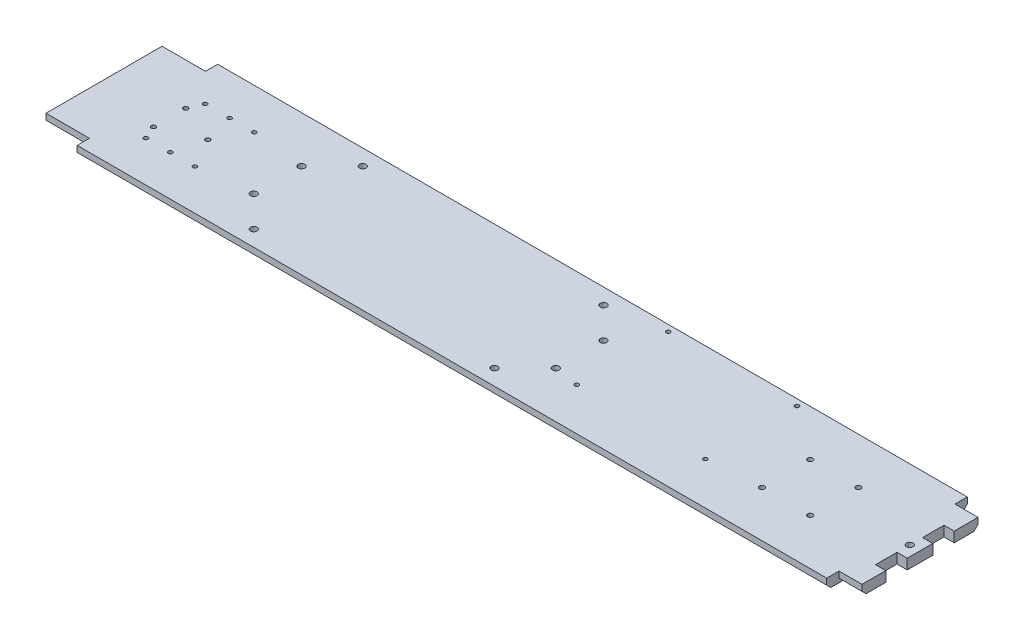
SolidWorks part; units mm, degrees
ref_plane "Front Plane" through (0, 0, 0) normal (0, 0, 1) x (1, 0, 0)
ref_plane "Top Plane" through (0, 0, 0) normal (0, 1, 0) x (1, 0, 0)
ref_plane "Right Plane" through (0, 0, 0) normal (1, 0, 0) x (0, 0, -1)
sketch "Sketch1" plane through (0, 0, 0) normal (0, 1, 0) x (1, 0, 0)
  line L1 (-260, 43.688) -> (260, 43.688)
  line L2 (-260, 43.688) -> (-260, -43.688)
  line L3 (-260, -43.688) -> (260, -43.688)
  line L4 (260, 43.688) -> (260, -43.688)
  point P4 (0, -43.688)
  point P6 (-260, 0)
  dimension "D1" = 520
  dimension "D2" = 87.376
extrude "Boss-Extrude1" add sketch "Sketch1" along normal blind 6.35
sketch "Sketch3" plane through (0, 6.35, 0) normal (0, 1, 0) x (1, 0, 0)
  line L1 (-260, 43.688) -> (-233, 43.688)
  line L2 (-260, 43.688) -> (-260, 36.068)
  line L3 (-260, 36.068) -> (-233, 36.068)
  line L4 (-233, 43.688) -> (-233, 36.068)
  line L5 (-260, -43.688) -> (-233, -43.688)
  line L6 (-260, -43.688) -> (-260, -36.068)
  line L7 (-260, -36.068) -> (-233, -36.068)
  line L8 (-233, -43.688) -> (-233, -36.068)
  line L9 (260, -43.688) -> (233, -43.688)
  line L10 (260, -43.688) -> (260, -36.068)
  line L11 (260, -36.068) -> (233, -36.068)
  line L12 (233, -43.688) -> (233, -36.068)
  line L13 (260, 43.688) -> (233, 43.688)
  line L14 (260, 43.688) -> (260, 36.068)
  line L15 (260, 36.068) -> (233, 36.068)
  line L16 (233, 43.688) -> (233, 36.068)
  dimension "D1" = 27
  dimension "D2" = 7.62
extrude "Cut-Extrude2" cut sketch "Sketch3" against normal through all
sketch "Sketch4" plane through (0, 6.35, 0) normal (0, 1, 0) x (1, 0, 0)
  line L0 (-260, 36.068) -> (-260, -36.068) construction
  line L1 (70.2, 14.0335) -> (209.9, 14.0335)
  line L2 (70.2, 14.0335) -> (70.2, -14.0335)
  line L3 (70.2, -14.0335) -> (209.9, -14.0335)
  line L4 (209.9, 14.0335) -> (209.9, -14.0335)
  point P4 (70.2, 0)
  point P7 (-260, 0)
  dimension "D1" = 28.067
  dimension "D2" = 139.7
  dimension "D3" = 330.2
extrude "Cut-Extrude3" [suppressed] cut sketch "Sketch4" against normal through all
sketch "Sketch5" [suppressed] plane through (0, 6.35, 0) normal (0, 1, 0) x (1, 0, 0)
  line L0 (70.2, -14.0335) -> (209.9, -14.0335) construction
  line L1 (108.935, -23.5585) -> (134.335, -23.5585) construction
  line L2 (70.2, 14.0335) -> (70.2, -14.0335) construction
  circle A0 centre (108.935, -23.5585) radius 3.302
  circle A1 centre (134.335, -23.5585) radius 3.302
  point P7 (121.635, -23.5585)
  dimension "D2" = 6.604
  dimension "D1" = 25.4
  dimension "D3" = 9.525
  dimension "D4" = 51.435
extrude "Cut-Extrude4" [suppressed] cut sketch "Sketch5" against normal through all
sketch "Sketch6" plane through (0, 6.35, 0) normal (0, 1, 0) x (1, 0, 0)
  line L0 (260, -36.068) -> (233, -36.068) construction
  line L1 (260, 36.068) -> (247.3, 36.068)
  line L2 (260, 36.068) -> (260, -36.068)
  line L3 (260, -36.068) -> (247.3, -36.068)
  line L4 (247.3, 36.068) -> (247.3, -36.068)
  dimension "D1" = 12.7
extrude "Cut-Extrude5" cut sketch "Sketch6" against normal through all
sketch "Sketch7" plane through (0, 6.35, 0) normal (0, 1, 0) x (1, 0, 0)
  line L0 (233, -36.068) -> (233, -43.688) construction
  line L1 (-233, -43.688) -> (233, -43.688) construction
  line L2 (233, 43.688) -> (-233, 43.688) construction
  circle A0 centre (187.28, -40.386) radius 0.635
  circle A1 centre (172.04, -40.386) radius 0.635
  circle A2 centre (172.04, 40.386) radius 0.635
  circle A3 centre (187.28, 40.386) radius 0.635
  dimension "D1" = 1.27
  dimension "D2" = 15.24
  dimension "D3" = 45.72
  dimension "D4" = 3.302
  dimension "D5" = 3.302
extrude "Cut-Extrude6" [suppressed] cut sketch "Sketch7" against normal through all
chamfer "Chamfer1" distance 2.54 angle 45 6 edges at (240.15, 0, 36.068) (240.15, 0, -36.068) (0, 0, -43.688) (0, 0, 43.688) (-246.5, 0, 36.068) (-246.5, 0, -36.068)
sketch "Sketch8" plane through (0, 6.35, 0) normal (0, 1, 0) x (1, 0, 0)
  line L0 (-219.2, 10) -> (-219.2, -10) construction
  line L1 (-195.5, 0) -> (-219.2, 0) construction
  line L2 (-260, 36.068) -> (-260, -36.068) construction
  circle A0 centre (-219.2, 10) radius 1.4
  circle A1 centre (-219.2, -10) radius 1.4
  circle A2 centre (-195.5, 0) radius 1.4
  point P6 (-219.2, 0)
  point P10 (-260, 0)
  dimension "D4" = 2.8
  dimension "D1" = 20
  dimension "D2" = 23.7
  dimension "D3" = 40.8
extrude "Cut-Extrude7" cut sketch "Sketch8" against normal through all
sketch "Sketch9" plane through (0, 6.35, 0) normal (0, 1, 0) x (1, 0, 0)
  line L0 (-152.05, 14.84) -> (-152.05, -14.84) construction
  line L1 (-133, 33.89) -> (-133, -33.89) construction
  line L2 (-260, 36.068) -> (-260, -36.068) construction
  circle A0 centre (-133, 33.89) radius 2.05
  circle A1 centre (-152.05, 14.84) radius 2.05
  circle A2 centre (-152.05, -14.84) radius 2.05
  circle A3 centre (-133, -33.89) radius 2.05
  circle A4 centre (16.68, 33.89) radius 2.05
  circle A5 centre (35.73, 14.84) radius 2.05
  circle A6 centre (35.73, -14.84) radius 2.05
  circle A7 centre (16.68, -33.89) radius 2.05
  point P16 (-133, 0)
  point P17 (-152.05, 0)
  point P20 (-260, 0)
  dimension "D1" = 4.1
  dimension "D2" = 29.68
  dimension "D3" = 67.78
  dimension "D4" = 19.05
  dimension "D5" = 19.05
  dimension "D6" = 149.68
  dimension "D7" = 107.95
extrude "Cut-Extrude8" cut sketch "Sketch9" against normal through all
sketch "Sketch10" plane through (0, 6.35, 0) normal (0, 1, 0) x (1, 0, 0)
  line L0 (-215.55, 18.415) -> (-215.55, -18.415) construction
  line L1 (-260, 36.068) -> (-260, -36.068) construction
  circle A0 centre (-200.31, -18.415) radius 1.27
  circle A1 centre (-215.55, -18.415) radius 1.27
  circle A2 centre (-200.31, 18.415) radius 1.27
  circle A3 centre (-215.55, 18.415) radius 1.27
  circle A4 centre (-185.07, 18.415) radius 1.27
  circle A5 centre (-185.07, -18.415) radius 1.27
  point P10 (-215.55, 0)
  point P11 (-260, 0)
  dimension "D4" = 2.54
  dimension "D5" = 2.54
  dimension "D6" = 2.54
  dimension "D1" = 44.45
  dimension "D2" = 15.24
  dimension "D3" = 36.83
  dimension "D7" = 15.24
extrude "Cut-Extrude9" cut sketch "Sketch10" against normal through all
sketch "Sketch11" plane through (0, 6.35, 0) normal (0, 1, 0) x (1, 0, 0)
  line L0 (247.3, 36.068) -> (247.3, -36.068) construction
  circle A0 centre (240.95, 0) radius 2.05
  point P4 (247.3, 0)
  dimension "D1" = 4.1
  dimension "D2" = 6.35
extrude "Cut-Extrude10" cut sketch "Sketch11" against normal through all
sketch "Sketch12" plane through (0, 6.35, 0) normal (0, 1, 0) x (1, 0, 0)
  line L0 (233, 43.688) -> (-233, 43.688) construction
  line L1 (-260, 36.068) -> (-260, -36.068) construction
  circle A0 centre (51.15, 39.688) radius 1.27
  circle A1 centre (131.15, 39.688) radius 1.27
  circle A2 centre (51.15, -17.312) radius 1.27
  circle A3 centre (131.15, -17.312) radius 1.27
  dimension "D1" = 2.54
  dimension "D2" = 80
  dimension "D3" = 57
  dimension "D4" = 4
  dimension "D5" = 311.15
extrude "Cut-Extrude11" cut sketch "Sketch12" against normal through all
sketch "Sketch13" plane through (0, 6.35, 0) normal (0, 1, 0) x (1, 0, 0)
  line L0 (247.3, 36.068) -> (247.3, -36.068) construction
  line L1 (247.3, -7.9375) -> (240.95, -7.9375)
  line L2 (247.3, -7.9375) -> (247.3, -21.2725)
  line L3 (247.3, -21.2725) -> (240.95, -21.2725)
  line L4 (240.95, -7.9375) -> (240.95, -21.2725)
  line L5 (247.3, 7.9375) -> (247.3, -7.9375) construction
  line L6 (247.3, 7.9375) -> (240.95, 7.9375)
  line L7 (247.3, 7.9375) -> (247.3, 21.2725)
  line L8 (247.3, 21.2725) -> (240.95, 21.2725)
  line L9 (240.95, 7.9375) -> (240.95, 21.2725)
  point P10 (247.3, 0)
  point P11 (247.3, 0)
  point P12 (240.95, 14.605)
  point P13 (240.95, -14.605)
  dimension "D1" = 29.21
  dimension "D2" = 6.35
  dimension "D3" = 13.335
extrude "Cut-Extrude12" cut sketch "Sketch13" against normal through all
sketch "Sketch14" plane through (0, 6.35, 0) normal (0, 1, 0) x (1, 0, 0)
  line L0 (-260, 36.068) -> (-260, -36.068) construction
  line L1 (233, 43.688) -> (-233, 43.688) construction
  circle A0 centre (164.053, 15) radius 1.6
  circle A1 centre (194.053, 15) radius 1.6
  circle A2 centre (164.053, -15) radius 1.6
  circle A3 centre (194.053, -15) radius 1.6
  dimension "D5" = 3.2
  dimension "D1" = 424.053
  dimension "D2" = 28.688
  dimension "D3" = 30
  dimension "D4" = 30
extrude "Cut-Extrude13" cut sketch "Sketch14" against normal through all
